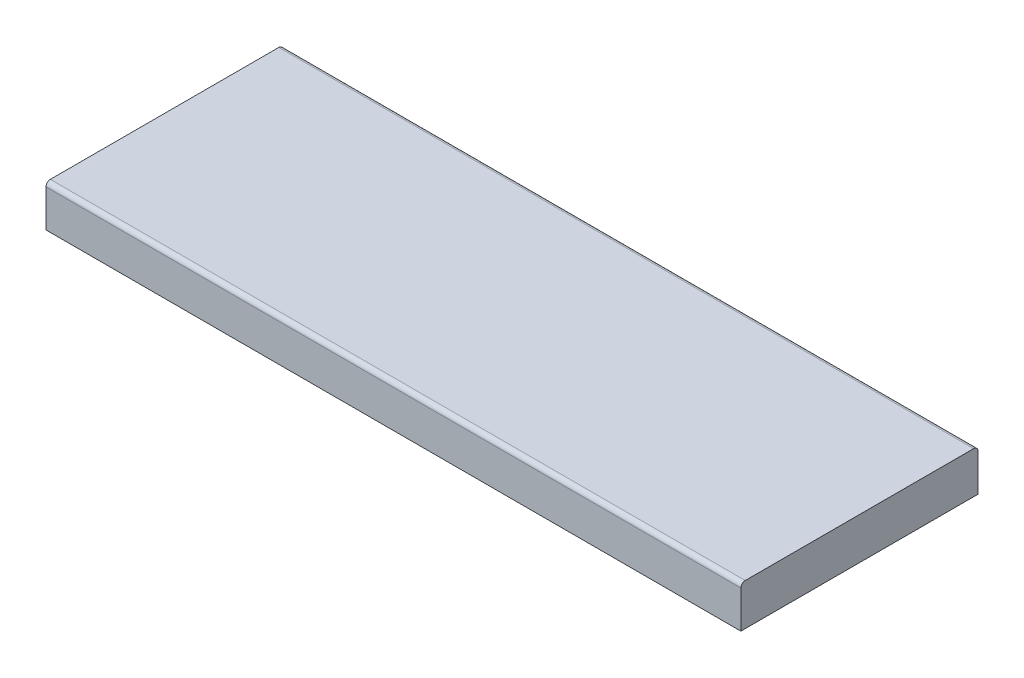
SolidWorks part; units mm, degrees
ref_plane "Front Plane" through (0, 0, 0) normal (0, 0, 1) x (1, 0, 0)
ref_plane "Top Plane" through (0, 0, 0) normal (0, 1, 0) x (1, 0, 0)
ref_plane "Right Plane" through (0, 0, 0) normal (1, 0, 0) x (0, 0, -1)
sketch "Sketch1" plane through (0, 0, 0) normal (0, 1, 0) x (1, 0, 0)
  line L1 (-80, -27.3) -> (80, -27.3)
  line L2 (-80, -27.3) -> (-80, 27.3)
  line L3 (-80, 27.3) -> (80, 27.3)
  line L4 (80, -27.3) -> (80, 27.3)
  line L5 (-80, -27.3) -> (80, 27.3) construction
  line L6 (-80, 27.3) -> (80, -27.3) construction
  point P0 (0, 0)
  dimension "D1" = 54.6
  dimension "D2" = 160
extrude "Boss-Extrude1" add sketch "Sketch1" along normal blind 9.6
fillet "Fillet1" radius 1 2 edges at (0, 9.6, -27.3) (0, 9.6, 27.3)
